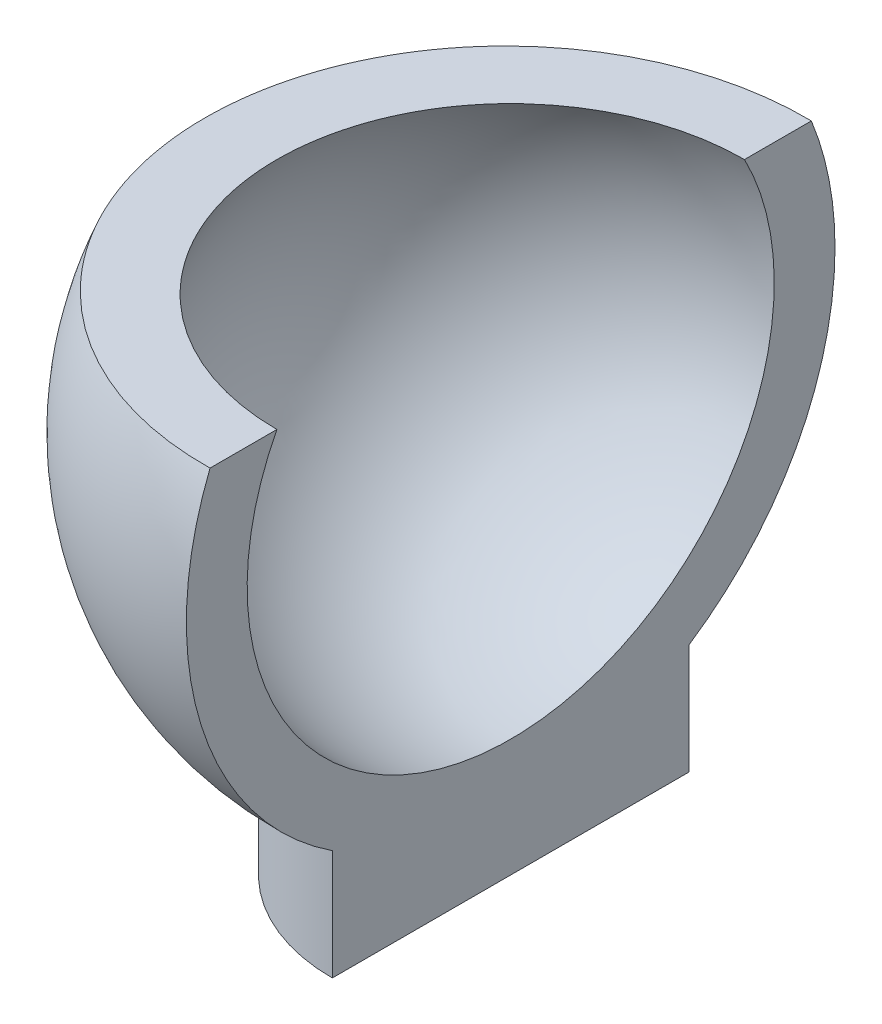
SolidWorks part; units mm, degrees
ref_plane "Front Plane" through (0, 0, 0) normal (0, 0, 1) x (1, 0, 0)
ref_plane "Top Plane" through (0, 0, 0) normal (0, 1, 0) x (1, 0, 0)
ref_plane "Right Plane" through (0, 0, 0) normal (1, 0, 0) x (0, 0, -1)
sketch "Sketch1" plane through (0, 0, 0) normal (0, 1, 0) x (1, 0, 0)
  line L0 (-66.6561, 0) -> (73.5603, 0) construction
  line L1 (-20.3185, 0) -> (19.6815, 0)
  arc A0 (-20.3185, 0) -> (19.6815, 0) centre (-0.3185, 0) cw
  dimension "D1" = 20
  dimension "D2" = 40
revolve "Revolve2" add sketch "Sketch1" angle 360 about L0
ref_plane "Plane1" through (0, 7.5, 0) normal (0, 1, 0) x (1, 0, 0)
sketch "Sketch2" plane through (0, 7.5, 0) normal (0, 1, 0) x (1, 0, 0)
  line L1 (21, -21) -> (-21, -21)
  line L2 (21, -21) -> (21, 21)
  line L3 (21, 21) -> (-21, 21)
  line L4 (-21, -21) -> (-21, 21)
  line L5 (21, -21) -> (-21, 21) construction
  line L6 (21, 21) -> (-21, -21) construction
  point P0 (0, 0)
  dimension "D1" = 42
  dimension "D2" = 42
extrude "Cut-Extrude1" cut sketch "Sketch2" along normal blind 20
sketch "Sketch3" plane through (0, 0, 0) normal (0, 0, 1) x (1, 0, 0)
  line L0 (-20.3185, 0) -> (19.6815, 0) construction
  line L1 (16.25, 0) -> (-16.25, 0)
  arc A0 (-18.859, 7.5) -> (18.222, 7.5) centre (-0.3185, 0) ccw construction
  arc A1 (-16.25, 0) -> (16.25, 0) centre (0, 0) ccw
  dimension "D1" = 32.5
revolve "Cut-Revolve1" cut sketch "Sketch3" angle 360 about L0
ref_plane "Plane2" through (0, -20, 0) normal (0, 1, 0) x (1, 0, 0)
sketch "Sketch4" plane through (0, -20, 0) normal (0, 1, 0) x (1, 0, 0)
  circle A0 centre (0, 0) radius 11
  dimension "D1" = 22
extrude "Boss-Extrude1" add sketch "Sketch4" along normal mid plane 7
sketch "Sketch5" plane through (0, -23.5, 0) normal (0, -1, 0) x (1, 0, 0)
  line L1 (37.9421, -21.0146) -> (0, -21.0146)
  line L2 (37.9421, -21.0146) -> (37.9421, 21.0146)
  line L3 (37.9421, 21.0146) -> (0, 21.0146)
  line L4 (0, -21.0146) -> (0, 21.0146)
  line L5 (37.9421, -21.0146) -> (0, 21.0146) construction
  line L6 (37.9421, 21.0146) -> (0, -21.0146) construction
  point P0 (18.971, 0)
extrude "Cut-Extrude2" cut sketch "Sketch5" against normal blind 40
